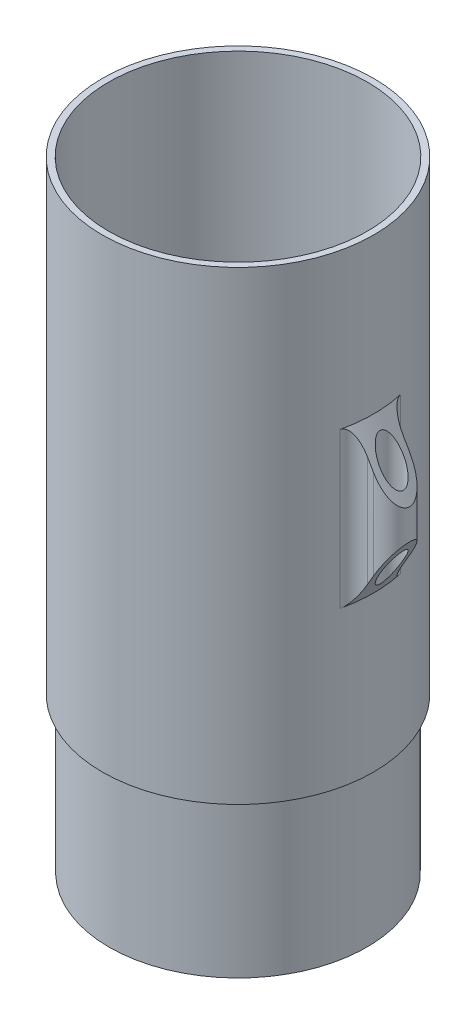
SolidWorks part; units mm, degrees
ref_plane "Front Plane" through (0, 0, 0) normal (0, 0, 1) x (1, 0, 0)
ref_plane "Top Plane" through (0, 0, 0) normal (0, 1, 0) x (1, 0, 0)
ref_plane "Right Plane" through (0, 0, 0) normal (1, 0, 0) x (0, 0, -1)
sketch "Sketch1" plane through (0, 0, 0) normal (0, 0, 1) x (1, 0, 0)
  line L0 (0, 0) -> (0, 54.0332) construction
  line L1 (-20.0787, -6.8588) -> (-20.0787, 20.445)
  line L2 (-20.0787, 20.445) -> (-21.1836, 24.5685)
  line L3 (-21.1836, 24.5685) -> (-21.1836, 94.7412)
  line L4 (-21.1836, 94.7412) -> (-22.225, 94.7412)
  line L5 (-22.225, 94.7412) -> (-22.225, 18.5412)
  line L6 (-22.225, 18.5412) -> (-21.1201, 18.5412)
  line L7 (-21.1201, 18.5412) -> (-21.1201, -6.8588)
  line L8 (-21.1201, -6.8588) -> (-20.0787, -6.8588)
  dimension "D1" = 42.2402
  dimension "D2" = 44.45
  dimension "D3" = 25.4
  dimension "D4" = 101.6
  dimension "D5" = 1.0414
  dimension "D6" = 1.0414
  dimension "D7" = 15
revolve "Revolve1" add sketch "Sketch1" angle 360 about L0
sketch "Sketch2" plane through (0, 94.7412, 0) normal (0, 1, 0) x (1, 0, 0)
  line L0 (25.1714, 2.9464) -> (22.0288, 2.9464)
  line L1 (25.1714, -2.9464) -> (22.0288, -2.9464)
  circle A0 centre (25.1714, 0) radius 1.905
  arc A1 (25.1714, -2.9464) -> (25.1714, 2.9464) centre (25.1714, 0) ccw
  circle A2 centre (0, 0) radius 22.225 construction
  arc A3 (22.0288, -2.9464) -> (22.0288, 2.9464) centre (0, 0) ccw
  dimension "D1" = 3.81
  dimension "D3" = 1.0414
  dimension "D2" = 25.1714
extrude "Boss-Extrude1" add sketch "Sketch2" against normal blind 25.4 from offset 25.4
fillet "Fillet1" radius 2.54 2 edges at (22.0288, 56.6412, -2.9464) (22.0288, 56.6412, 2.9464)
sketch "Sketch3" plane through (0, 0, 0) normal (0, 0, 1) x (1, 0, 0)
  line L0 (22.225, 69.3412) -> (28.1178, 59.1346)
  line L1 (28.1178, 43.9412) -> (28.1178, 69.3412) construction
  line L2 (22.225, 69.3412) -> (28.1178, 69.3412)
  line L3 (28.1178, 69.3412) -> (28.1178, 59.1346)
  line L4 (22.225, 43.9412) -> (28.1178, 54.1478)
  line L5 (28.1178, 54.1478) -> (28.1178, 43.9412)
  line L6 (28.1178, 43.9412) -> (22.225, 43.9412)
  dimension "D1" = 60
revolve "Cut-Revolve2" cut sketch "Sketch3" angle 360 about axis through (0, 0, 0) along (0, -1, 0)
